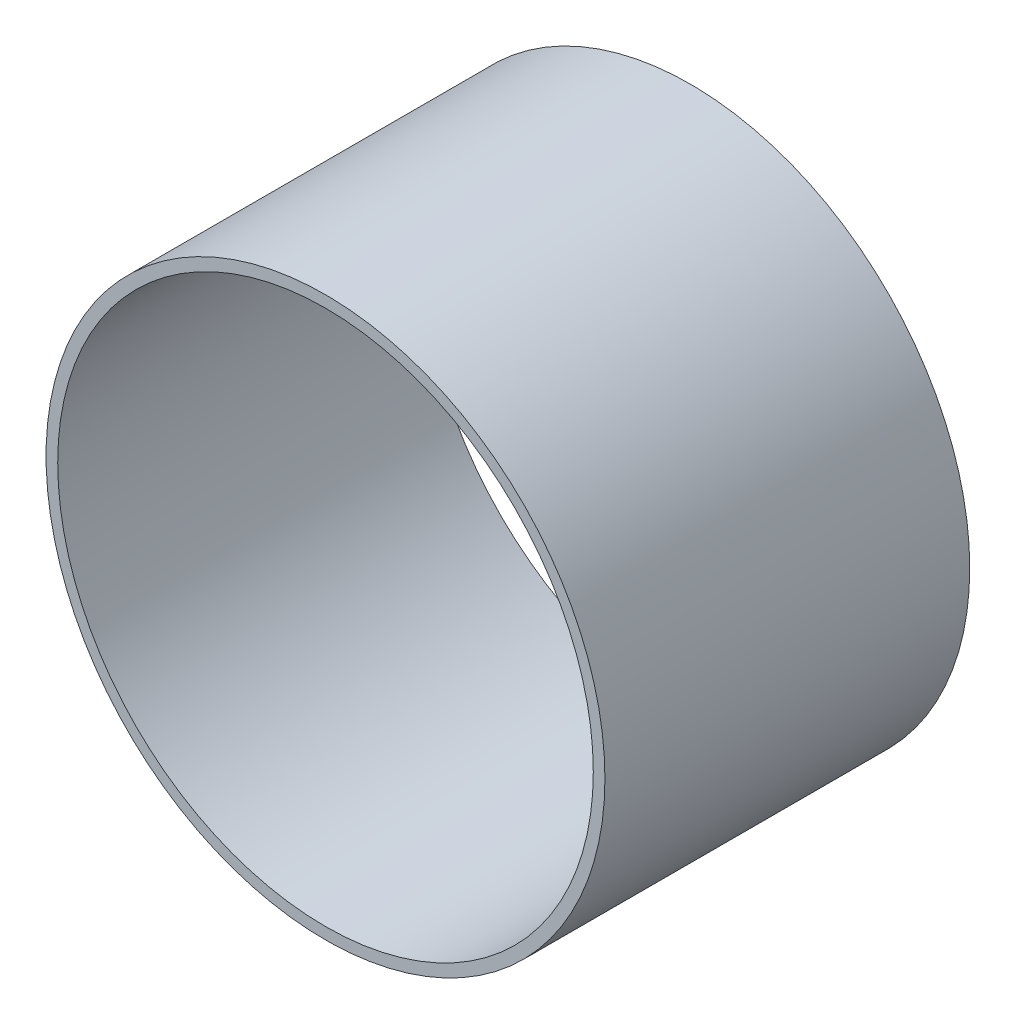
SolidWorks part; units mm, degrees
ref_plane "Front" through (0, 0, 0) normal (0, 0, 1) x (1, 0, 0)
ref_plane "Top" through (0, 0, 0) normal (0, 1, 0) x (1, 0, 0)
ref_plane "Right" through (0, 0, 0) normal (1, 0, 0) x (0, 0, -1)
sketch "Sketch1" plane through (0, 0, 0) normal (0, 0, 1) x (1, 0, 0)
  circle A0 centre (0, 0) radius 109.5375
  circle A1 centre (0, 0) radius 114.3
  dimension "D1" = 219.075
  dimension "D2" = 228.6
extrude "Boss-Extrude1" add sketch "Sketch1" along normal mid plane 149.225
